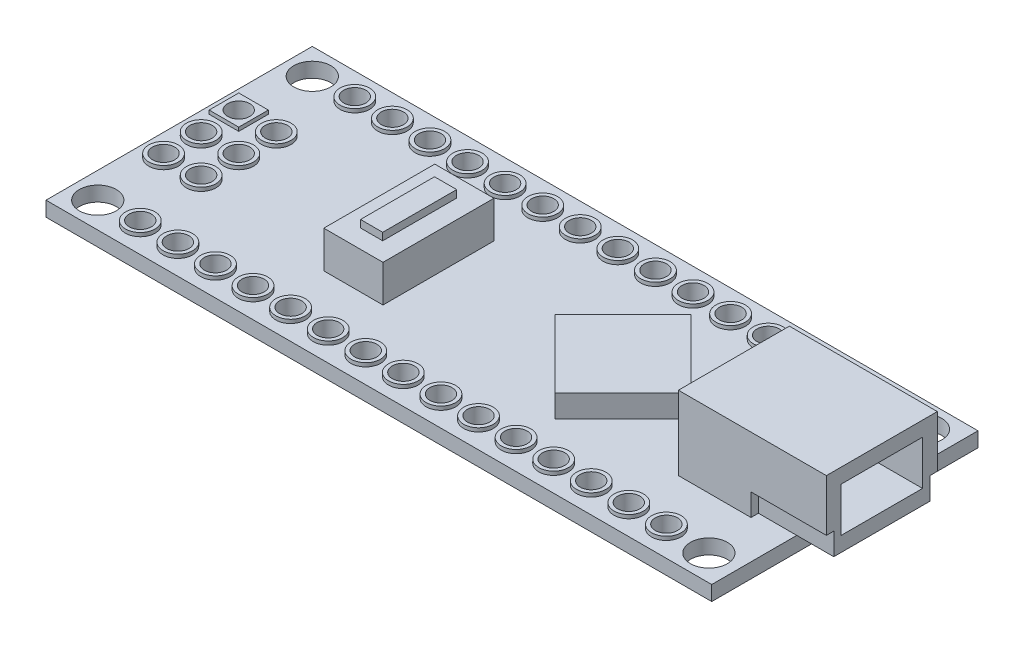
SolidWorks part; units mm, degrees
ref_plane "Front Plane" through (0, 0, 0) normal (0, 0, 1) x (1, 0, 0)
ref_plane "Top Plane" through (0, 0, 0) normal (0, 1, 0) x (1, 0, 0)
ref_plane "Right Plane" through (0, 0, 0) normal (1, 0, 0) x (0, 0, -1)
sketch "Sketch1" plane through (0, 0, 0) normal (0, 1, 0) x (1, 0, 0)
  line L0 (0, 16.7896) -> (0, -16.7896) construction
  line L1 (-22.4051, 9) -> (22.5949, 9)
  line L2 (-22.4051, 9) -> (-22.4051, -9)
  line L3 (-22.4051, -9) -> (22.5949, -9)
  line L4 (22.5949, 9) -> (22.5949, -9)
  line L7 (-38.803, 0) -> (38.803, 0) construction
  circle A0 centre (-20.6551, 7.25) radius 1.25
  circle A1 centre (20.6551, 7.25) radius 1.25
  circle A2 centre (20.6551, -7.25) radius 1.25
  circle A3 centre (-20.6551, -7.25) radius 1.25
  circle A4 centre (-17.7809, 7.25) radius 0.75
  circle A5 centre (-15.2409, 7.25) radius 0.75
  circle A8 centre (-10.1609, 7.25) radius 0.75
  circle A10 centre (-7.6209, 7.25) radius 0.75
  circle A11 centre (-5.0809, 7.25) radius 0.75
  circle A13 centre (-2.5409, 7.25) radius 0.75
  circle A14 centre (-12.7009, 7.25) radius 0.75
  circle A15 centre (-0.0009, 7.25) radius 0.75
  circle A16 centre (2.5409, 7.25) radius 0.75
  circle A17 centre (5.0809, 7.25) radius 0.75
  circle A18 centre (7.6209, 7.25) radius 0.75
  circle A19 centre (10.1609, 7.25) radius 0.75
  circle A20 centre (12.7009, 7.25) radius 0.75
  circle A21 centre (15.2409, 7.25) radius 0.75
  circle A22 centre (17.7809, 7.25) radius 0.75
  circle A23 centre (17.7809, -7.25) radius 0.75
  circle A24 centre (15.2409, -7.25) radius 0.75
  circle A25 centre (12.7009, -7.25) radius 0.75
  circle A26 centre (10.1609, -7.25) radius 0.75
  circle A27 centre (7.6209, -7.25) radius 0.75
  circle A28 centre (5.0809, -7.25) radius 0.75
  circle A29 centre (2.5409, -7.25) radius 0.75
  circle A30 centre (-0.0009, -7.25) radius 0.75
  circle A31 centre (-2.5409, -7.25) radius 0.75
  circle A32 centre (-5.0809, -7.25) radius 0.75
  circle A33 centre (-7.6209, -7.25) radius 0.75
  circle A34 centre (-10.1609, -7.25) radius 0.75
  circle A35 centre (-12.7009, -7.25) radius 0.75
  circle A36 centre (-15.2409, -7.25) radius 0.75
  circle A37 centre (-17.7809, -7.25) radius 0.75
  point P0 (0, 0)
  point P9 (0, 0)
  point P12 (0, 0)
  dimension "D3" = 2.5
  dimension "D4" = 1.75
  dimension "D6" = 1.5
  dimension "D9" = 1.5
  dimension "D1" = 45
  dimension "D2" = 18
  dimension "D5" = 1.75
  dimension "D7" = 22.5958
  dimension "D8" = 1.75
  dimension "D10" = 1.75
  dimension "D11" = 2.54
  dimension "D12" = 1.75
  dimension "D13" = 1.75
  dimension "D14" = 1.75
  dimension "D15" = 1.75
  dimension "D16" = 1.75
  dimension "D17" = 1.75
  dimension "D18" = 2.54
  dimension "D19" = 2.54
  dimension "D20" = 2.54
  dimension "D21" = 2.54
  dimension "D22" = 2.54
  dimension "D23" = 2.54
extrude "Boss-Extrude1" add sketch "Sketch1" against normal blind 1 contours A15 | A30 | A28 | A23 | A2 | L2 L3 L4 L1 | A1 | A22 | A21 | A20 | A19 | A18 | A17 | A16 | A13 | A11 | A10 | A8 | A14 | A5 | A4 | A0 | A3 | A37 | A36 | A35 | A34 | A33 | A32 | A31 | A29 | A27 | A26 | A25 | A24
sketch "Sketch2" plane through (0, 0, 0) normal (0, 1, 0) x (1, 0, 0)
  line L0 (-40.0987, 0) -> (40.0987, 0) construction
  line L1 (22.5949, 9) -> (22.5949, -9) construction
  line L2 (15.0949, 3.75) -> (25.0949, 3.75)
  line L3 (15.0949, 3.75) -> (15.0949, -3.75)
  line L4 (15.0949, -3.75) -> (25.0949, -3.75)
  line L5 (25.0949, 3.75) -> (25.0949, -3.75)
  line L6 (15.0949, 3.75) -> (25.0949, -3.75) construction
  line L7 (15.0949, -3.75) -> (25.0949, 3.75) construction
  point P0 (20.0949, 0)
  point P4 (0, 0)
  dimension "D1" = 7.5
  dimension "D2" = 10
  dimension "D3" = 2.5
extrude "Boss-Extrude2" add sketch "Sketch2" along normal blind 5 separate body
ref_plane "Plane1" through (25, 0, 0) normal (1, 0, 0) x (0, 0, -1)
sketch "Sketch4" plane through (25, 0, 0) normal (1, 0, 0) x (0, 0, -1)
  line L0 (0, 7.0847) -> (0, -7.0847) construction
  line L2 (-8.6097, 2.5) -> (8.6097, 2.5) construction
  line L3 (-3.75, 5) -> (3.75, 5) construction
  line L5 (-2.75, 4) -> (2.75, 4)
  line L6 (-2.75, 4) -> (-2.75, 1)
  line L7 (-2.75, 1) -> (2.75, 1)
  line L8 (2.75, 4) -> (2.75, 1)
  line L9 (-2.75, 4) -> (2.75, 1) construction
  line L10 (-2.75, 1) -> (2.75, 4) construction
  point P4 (0, 0)
  point P8 (0, 2.5)
  point P10 (0, 2.5)
  dimension "D1" = 2.5
  dimension "D2" = 5.5
  dimension "D3" = 1
extrude "Cut-Extrude1" cut sketch "Sketch4" against normal blind 7.5 and the other way through all
sketch "Sketch6" plane through (25, 0, 0) normal (1, 0, 0) x (0, 0, -1)
  line L0 (-3.75, 5) -> (-3.75, 0) construction
  line L1 (-3.75, 1.5) -> (-3.25, 1.5)
  line L2 (-3.75, 1.5) -> (-3.75, 0)
  line L3 (-3.75, 0) -> (-3.25, 0)
  line L4 (-3.25, 1.5) -> (-3.25, 0)
  line L5 (-3.75, 0) -> (3.75, 0) construction
  line L6 (0, 9.1639) -> (0, -9.1639) construction
  line L8 (3.75, 0) -> (3.25, 0)
  line L9 (3.75, 1.5) -> (3.75, 0)
  line L10 (3.75, 1.5) -> (3.25, 1.5)
  line L11 (3.25, 1.5) -> (3.25, 0)
  point P12 (0, 0)
  dimension "D1" = 1.5
  dimension "D2" = 0.5
extrude "Cut-Extrude2" cut sketch "Sketch6" against normal blind 5 and the other way through all
sketch "Sketch7" plane through (0, 0, 0) normal (0, 1, 0) x (1, 0, 0)
  line L0 (-44.6499, 0) -> (44.6499, 0) construction
  line L1 (7.5949, 15.0065) -> (7.5949, -13.7341) construction
  line L2 (22.5949, 9) -> (22.5949, -9) construction
  line L3 (7.5949, 4.6015) -> (2.9934, 0)
  line L4 (7.5949, -4.6015) -> (2.9934, 0)
  line L5 (7.5949, -4.6015) -> (12.1964, 0)
  line L6 (7.5949, 4.6015) -> (12.1964, 0)
  point P4 (0, 0)
  dimension "D1" = 15
extrude "Boss-Extrude3" add sketch "Sketch7" along normal blind 1.5 separate body
sketch "Sketch8" plane through (0, 0, 0) normal (0, 1, 0) x (1, 0, 0)
  line L0 (-37.5341, 0) -> (37.5341, 0) construction
  line L2 (-8.8766, 3.75) -> (-4.8766, 3.75)
  line L3 (-8.8766, 3.75) -> (-8.8766, -3.75)
  line L4 (-8.8766, -3.75) -> (-4.8766, -3.75)
  line L5 (-4.8766, 3.75) -> (-4.8766, -3.75)
  line L6 (-8.8766, 3.75) -> (-4.8766, -3.75) construction
  line L7 (-8.8766, -3.75) -> (-4.8766, 3.75) construction
  point P0 (-6.8766, 0)
  point P4 (0, 0)
  dimension "D1" = 7.5
  dimension "D2" = 4
extrude "Boss-Extrude4" add sketch "Sketch8" along normal blind 2.5
sketch "Sketch9" plane through (0, 0, 0) normal (0, 1, 0) x (1, 0, 0)
  line L0 (-28.5652, 0) -> (28.5652, 0) construction
  line L2 (-7.6444, 2.5) -> (-6.1444, 2.5)
  line L3 (-7.6444, 2.5) -> (-7.6444, -2.5)
  line L4 (-7.6444, -2.5) -> (-6.1444, -2.5)
  line L5 (-6.1444, 2.5) -> (-6.1444, -2.5)
  line L6 (-7.6444, 2.5) -> (-6.1444, -2.5) construction
  line L7 (-7.6444, -2.5) -> (-6.1444, 2.5) construction
  point P0 (-6.8944, 0)
  point P4 (0, 0)
  dimension "D1" = 1.5
  dimension "D2" = 5
extrude "Boss-Extrude5" add sketch "Sketch9" along normal blind 3 separate body
sketch "Sketch10" plane through (0, 0, 0) normal (0, 1, 0) x (1, 0, 0)
  line L0 (-34.3735, 0) -> (34.3735, 0) construction
  line L1 (-19.6466, 12.5121) -> (-19.6466, -12.5121) construction
  line L2 (-8.8766, 3.75) -> (-8.8766, -3.75) construction
  circle A0 centre (-18.3766, 0) radius 0.75
  circle A1 centre (-18.3766, 2.54) radius 0.75
  circle A2 centre (-18.3766, -2.54) radius 0.75
  circle A3 centre (-20.9166, 2.54) radius 0.75
  circle A4 centre (-20.9166, -2.54) radius 0.75
  circle A5 centre (-20.9166, 0) radius 0.75
  point P4 (0, 0)
  point P11 (-19.6466, 0)
  dimension "D1" = 1.5
  dimension "D2" = 1.5
  dimension "D3" = 2.54
  dimension "D4" = 1.27
  dimension "D5" = 9.5
extrude "Cut-Extrude3" cut sketch "Sketch10" against normal blind 3.5 and the other way through all
sketch "Sketch11" plane through (0, 0, 0) normal (0, 1, 0) x (1, 0, 0)
  line L0 (0, 14.3347) -> (0, -14.3347) construction
  line L1 (-31.1316, 0) -> (31.1316, 0) construction
  line L3 (-21.9166, 3.54) -> (-19.9166, 3.54)
  line L4 (-21.9166, 3.54) -> (-21.9166, 1.54)
  line L5 (-21.9166, 1.54) -> (-19.9166, 1.54)
  line L6 (-19.9166, 3.54) -> (-19.9166, 1.54)
  line L7 (-21.9166, 3.54) -> (-19.9166, 1.54) construction
  line L8 (-21.9166, 1.54) -> (-19.9166, 3.54) construction
  circle A0 centre (-17.7809, 7.25) radius 0.75
  circle A1 centre (-17.7809, 7.25) radius 1
  circle A2 centre (-15.2409, 7.25) radius 0.75
  circle A3 centre (-15.2409, 7.25) radius 1
  circle A4 centre (-12.7009, 7.25) radius 0.75
  circle A5 centre (-12.7009, 7.25) radius 1
  circle A6 centre (-10.1609, 7.25) radius 0.75
  circle A7 centre (-10.1609, 7.25) radius 1
  circle A8 centre (-7.6209, 7.25) radius 0.75
  circle A9 centre (-7.6209, 7.25) radius 1
  circle A10 centre (-5.0809, 7.25) radius 0.75
  circle A11 centre (-5.0809, 7.25) radius 1
  circle A12 centre (-2.5409, 7.25) radius 0.75
  circle A13 centre (-2.5409, 7.25) radius 1
  circle A14 centre (-0.0009, 7.25) radius 0.75
  circle A15 centre (-0.0009, 7.25) radius 1
  circle A16 centre (2.5409, 7.25) radius 1
  circle A17 centre (2.5409, 7.25) radius 0.75
  circle A18 centre (5.0809, 7.25) radius 1
  circle A19 centre (5.0809, 7.25) radius 0.75
  circle A20 centre (7.6209, 7.25) radius 1
  circle A21 centre (7.6209, 7.25) radius 0.75
  circle A22 centre (10.1609, 7.25) radius 1
  circle A23 centre (10.1609, 7.25) radius 0.75
  circle A24 centre (12.7009, 7.25) radius 1
  circle A25 centre (12.7009, 7.25) radius 0.75
  circle A26 centre (15.2409, 7.25) radius 1
  circle A27 centre (15.2409, 7.25) radius 0.75
  circle A28 centre (17.7809, 7.25) radius 1
  circle A29 centre (17.7809, 7.25) radius 0.75
  circle A30 centre (17.7809, -7.25) radius 1
  circle A31 centre (17.7809, -7.25) radius 0.75
  circle A32 centre (15.2409, -7.25) radius 1
  circle A33 centre (15.2409, -7.25) radius 0.75
  circle A34 centre (12.7009, -7.25) radius 1
  circle A35 centre (12.7009, -7.25) radius 0.75
  circle A36 centre (10.1609, -7.25) radius 1
  circle A37 centre (10.1609, -7.25) radius 0.75
  circle A38 centre (7.6209, -7.25) radius 1
  circle A39 centre (7.6209, -7.25) radius 0.75
  circle A40 centre (5.0809, -7.25) radius 1
  circle A41 centre (5.0809, -7.25) radius 0.75
  circle A42 centre (2.5409, -7.25) radius 1
  circle A43 centre (2.5409, -7.25) radius 0.75
  circle A44 centre (-0.0009, -7.25) radius 1
  circle A45 centre (-0.0009, -7.25) radius 0.75
  circle A46 centre (-2.5409, -7.25) radius 1
  circle A47 centre (-2.5409, -7.25) radius 0.75
  circle A48 centre (-5.0809, -7.25) radius 1
  circle A49 centre (-5.0809, -7.25) radius 0.75
  circle A50 centre (-7.6209, -7.25) radius 1
  circle A51 centre (-7.6209, -7.25) radius 0.75
  circle A52 centre (-10.1609, -7.25) radius 1
  circle A53 centre (-10.1609, -7.25) radius 0.75
  circle A54 centre (-12.7009, -7.25) radius 1
  circle A55 centre (-12.7009, -7.25) radius 0.75
  circle A56 centre (-15.2409, -7.25) radius 1
  circle A57 centre (-15.2409, -7.25) radius 0.75
  circle A58 centre (-17.7809, -7.25) radius 1
  circle A59 centre (-17.7809, -7.25) radius 0.75
  circle A60 centre (-18.3766, 2.54) radius 0.75
  circle A61 centre (-20.9166, 2.54) radius 0.75
  circle A62 centre (-18.3766, 0) radius 0.75
  circle A63 centre (-20.9166, 0) radius 0.75
  circle A64 centre (-18.3766, -2.54) radius 0.75
  circle A65 centre (-20.9166, -2.54) radius 0.75
  circle A66 centre (-18.3766, 2.54) radius 1
  circle A68 centre (-18.3766, 0) radius 1
  circle A69 centre (-20.9166, 0) radius 1
  circle A70 centre (-20.9166, -2.54) radius 1
  circle A71 centre (-18.3766, -2.54) radius 1
  point P4 (0, 0)
  point P8 (0, 0)
  dimension "D1" = 2
  dimension "D2" = 2
  dimension "D3" = 2
  dimension "D4" = 2
  dimension "D5" = 2
  dimension "D6" = 2
  dimension "D7" = 2
  dimension "D8" = 2
  dimension "D9" = 2
  dimension "D10" = 2
  dimension "D11" = 2
  dimension "D12" = 2
  dimension "D13" = 2
extrude "Boss-Extrude6" add sketch "Sketch11" along normal blind 0.25
